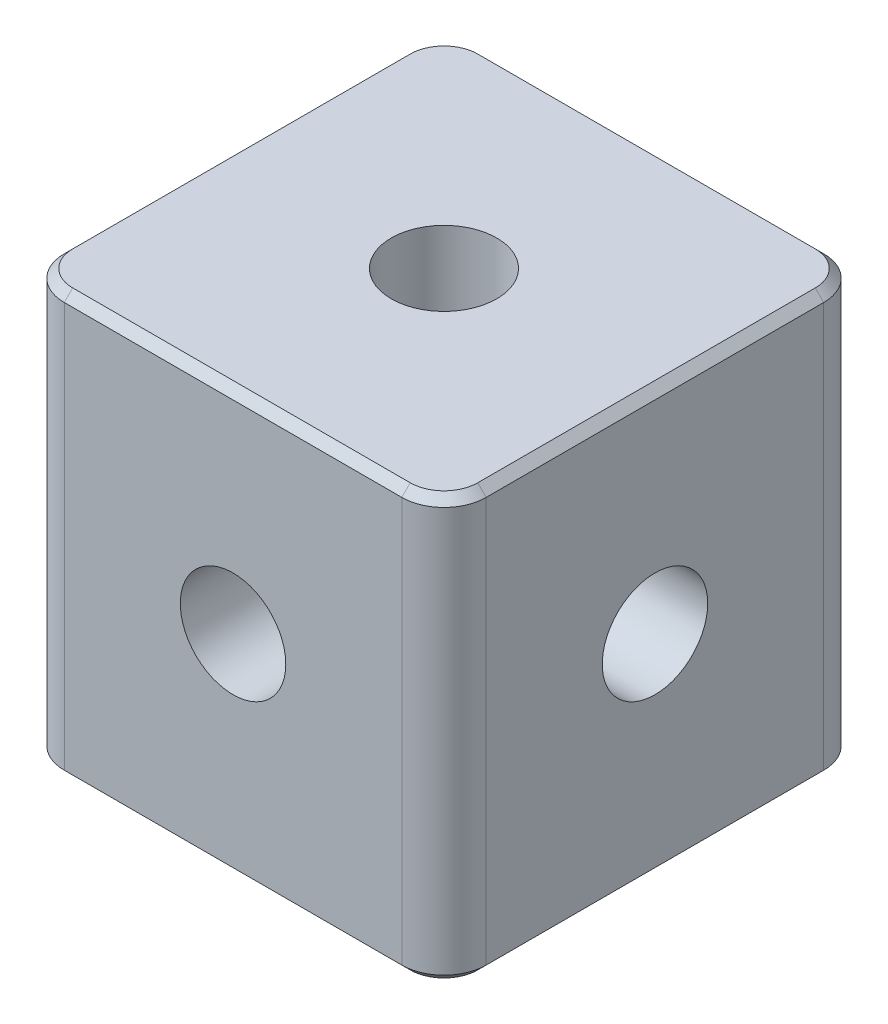
SolidWorks part; units mm, degrees
material "6061 合金"
ref_plane "前视基准面" through (0, 0, 0) normal (0, 0, 1) x (1, 0, 0)
ref_plane "上视基准面" through (0, 0, 0) normal (0, 1, 0) x (1, 0, 0)
ref_plane "右视基准面" through (0, 0, 0) normal (1, 0, 0) x (0, 0, -1)
sketch "草图1" plane through (0, 0, 0) normal (0, 1, 0) x (1, 0, 0)
  line L1 (-5, -5) -> (5, -5)
  line L2 (-5, -5) -> (-5, 5)
  line L3 (-5, 5) -> (5, 5)
  line L4 (5, -5) -> (5, 5)
  line L5 (0, 5) -> (0, -5) construction
  line L6 (-5, 0) -> (5, 0) construction
  point P0 (0, 0)
  dimension "D1" = 10
extrude "凸台-拉伸1" add sketch "草图1" along normal mid plane 10
hole_wizard "M3 螺纹孔1" positions "草图2" profile "草图3" tap size "M3" standard "GB" end condition through all
sketch "草图2" plane through (0, 5, 0) normal (0, 1, 0) x (1, 0, 0)
  point P0 (0, 0)
sketch "草图3" plane through (0, 5, 0) normal (1, 0, 0) x (0, 0, 1)
  line L0 (0, 0) -> (0, 10)
  line L1 (0, 10) -> (1.25, 10)
  line L2 (1.25, 10) -> (1.25, 0)
  line L5 (1.25, 0) -> (0, 0)
  line L11 (0, -6.35) -> (0, 107.95) construction
  dimension "通孔螺纹孔钻头直径" = 2.5
  dimension "通孔螺纹孔钻头深度" = 10
cosmetic thread "孔螺蚊线1" parameters "D2"=3
hole_wizard "M3 螺纹孔2" positions "草图4" profile "草图5" tap size "M3" standard "GB" end condition through all
sketch "草图4" plane through (0, 0, 5) normal (0, 0, 1) x (1, 0, 0)
  point P0 (0, 0)
sketch "草图5" plane through (0, 0, 5) normal (1, 0, 0) x (0, -1, 0)
  line L0 (0, 0) -> (0, 10)
  line L1 (0, 10) -> (1.25, 10)
  line L2 (1.25, 10) -> (1.25, 0)
  line L5 (1.25, 0) -> (0, 0)
  line L11 (0, -6.35) -> (0, 107.95) construction
  dimension "通孔螺纹孔钻头直径" = 2.5
  dimension "通孔螺纹孔钻头深度" = 10
cosmetic thread "孔螺蚊线2" parameters "D2"=3
hole_wizard "M3 螺纹孔3" positions "草图6" profile "草图7" tap size "M3" standard "GB" end condition through all
sketch "草图6" plane through (5, 0, 0) normal (1, 0, 0) x (0, 0, -1)
  point P0 (0, 0)
sketch "草图7" plane through (5, 0, 0) normal (0, 1, 0) x (0, 0, -1)
  line L0 (0, 0) -> (0, 10)
  line L1 (0, 10) -> (1.25, 10)
  line L2 (1.25, 10) -> (1.25, 0)
  line L5 (1.25, 0) -> (0, 0)
  line L11 (0, -6.35) -> (0, 107.95) construction
  dimension "通孔螺纹孔钻头直径" = 2.5
  dimension "通孔螺纹孔钻头深度" = 10
cosmetic thread "孔螺蚊线3" parameters "D2"=3
fillet "圆角1" radius 1 4 edges at (5, 0, -5) (5, 0, 5) (-5, 0, 5) (-5, 0, -5)
chamfer "倒角1" distance 0.2 angle 45 16 edges at (5, -5, 0) (4.7071, -5, -4.7071) (4.7071, -5, 4.7071) (0, -5, -5) (0, -5, 5) (-4.7071, -5, -4.7071) (-4.7071, -5, 4.7071) (-5, -5, 0) (5, 5, 0) (4.7071, 5, -4.7071) (4.7071, 5, 4.7071) (0, 5, -5) (0, 5, 5) (-4.7071, 5, -4.7071) (-4.7071, 5, 4.7071) (-5, 5, 0)
